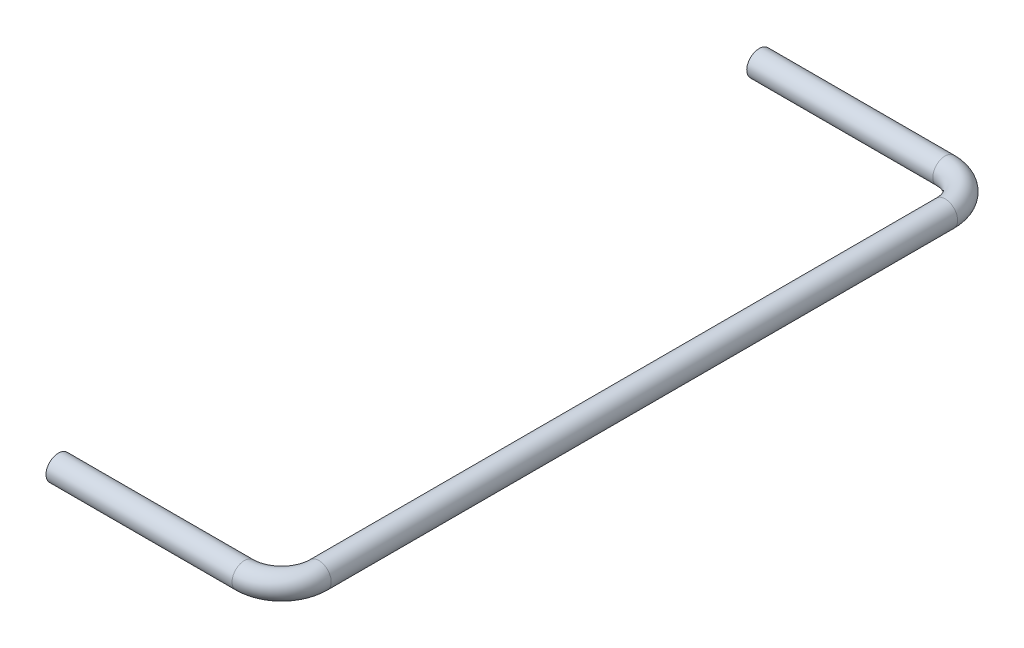
SolidWorks part; units mm, degrees
ref_plane "Спереди" through (0, 0, 0) normal (0, 0, 1) x (1, 0, 0)
ref_plane "Сверху" through (0, 0, 0) normal (0, 1, 0) x (1, 0, 0)
ref_plane "Справа" through (0, 0, 0) normal (1, 0, 0) x (0, 0, -1)
sketch "Эскиз1" plane through (0, 0, 0) normal (1, 0, 0) x (0, 0, -1)
  circle A0 centre (0, 0) radius 1
sketch3d "Трехмерный эскиз1"
  line L0 (0, 0, 0) -> (15, 0, 0)
  line L1 (18, 0, -3) -> (18, 0, -53.5)
  line L2 (15, 0, -56.5) -> (0, 0, -56.5)
  arc A0 (15, 0, 0) -> (18, 0, -3) centre (15, 0, -3) ccw
  arc A1 (18, 0, -53.5) -> (15, 0, -56.5) centre (15, 0, -53.5) ccw
  point P7 (18, 0, 0)
  point P8 (15, 3, -3)
  point P11 (18, 0, -56.5)
  point P12 (15, 3, -53.5)
  dimension "D1" = 3
sweep "По траектории1" add profiles "Эскиз1" path "Трехмерный эскиз1"
